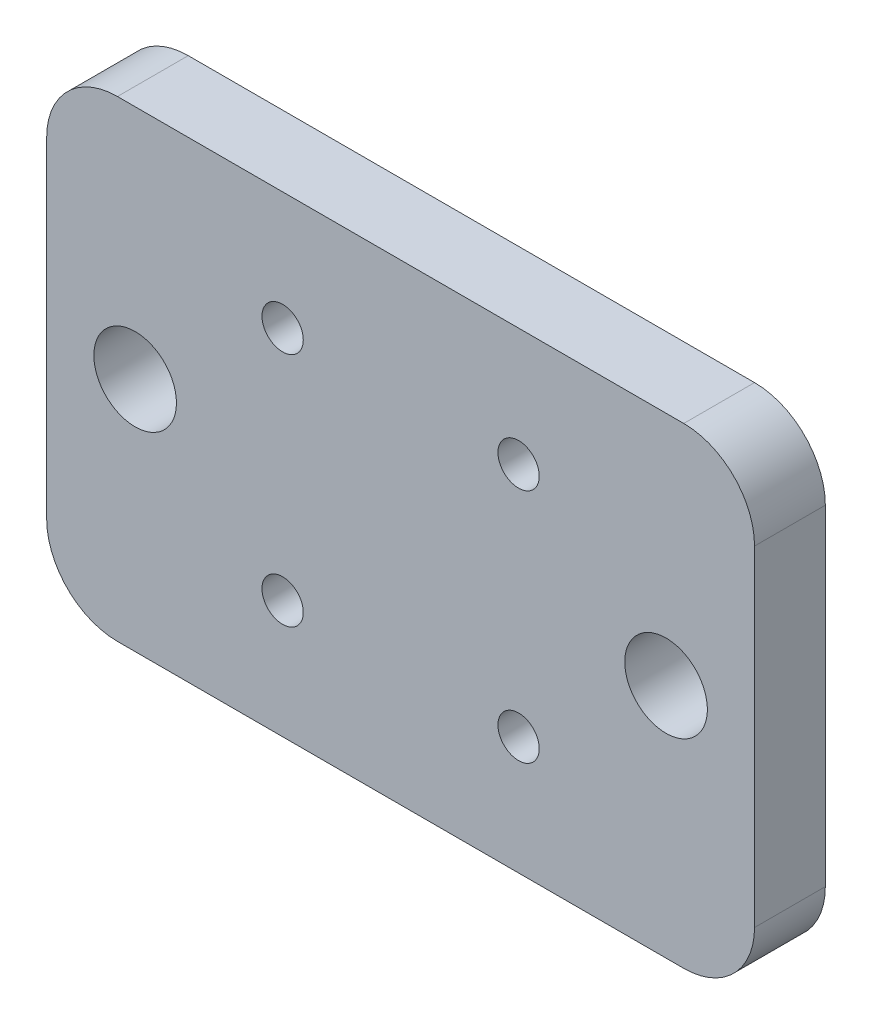
SolidWorks part; units mm, degrees
ref_plane "Plan de face" through (0, 0, 0) normal (0, 0, 1) x (1, 0, 0)
ref_plane "Plan de dessus" through (0, 0, 0) normal (0, 1, 0) x (1, 0, 0)
ref_plane "Plan de droite" through (0, 0, 0) normal (1, 0, 0) x (0, 0, -1)
sketch "Esquisse1" plane through (0, 0, 0) normal (0, 0, 1) x (1, 0, 0)
  line L1 (0, 0) -> (60, 0)
  line L2 (0, 0) -> (0, 40)
  line L3 (0, 40) -> (60, 40)
  line L4 (60, 0) -> (60, 40)
  dimension "D1" = 60
  dimension "D2" = 40
extrude "Boss.-Extru.1" add sketch "Esquisse1" along normal blind 6
sketch "Esquisse2" plane through (0, 0, 6) normal (0, 0, 1) x (1, 0, 0)
  line L0 (30, 0) -> (30, 40) construction
  line L1 (0, 0) -> (60, 0) construction
  line L2 (60, 40) -> (0, 40) construction
  line L3 (60, 20) -> (0, 20) construction
  line L4 (60, 0) -> (60, 40) construction
  line L5 (0, 40) -> (0, 0) construction
  circle A0 centre (20, 30) radius 1.75
  circle A1 centre (40, 30) radius 1.75
  circle A2 centre (40, 10) radius 1.75
  circle A3 centre (20, 10) radius 1.75
  circle A4 centre (7.5, 20) radius 3.5
  circle A5 centre (52.5, 20) radius 3.5
  dimension "D1" = 3.5
  dimension "D3" = 20
  dimension "D4" = 7
  dimension "D2" = 20
  dimension "D5" = 45
extrude "Enlèv. mat.-Extru.1" cut sketch "Esquisse2" against normal through all both and the other way through all
fillet "Congé1" radius 6 4 edges at (60, 40, 3) (60, 0, 3) (0, 0, 3) (0, 40, 3)
